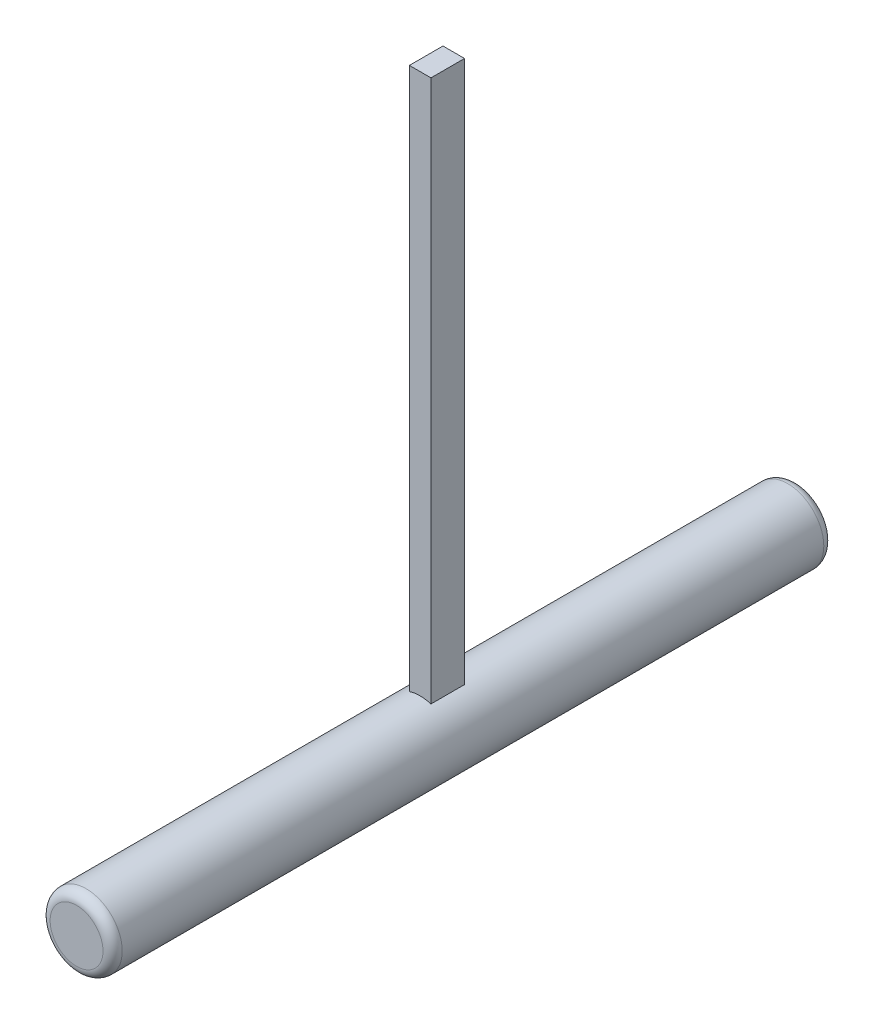
SolidWorks part; units mm, degrees
ref_plane "Front Plane" through (0, 0, 0) normal (0, 0, 1) x (1, 0, 0)
ref_plane "Top Plane" through (0, 0, 0) normal (0, 1, 0) x (1, 0, 0)
ref_plane "Right Plane" through (0, 0, 0) normal (1, 0, 0) x (0, 0, -1)
sketch "Sketch1" plane through (0, 0, 0) normal (0, 0, 1) x (1, 0, 0)
  circle A0 centre (0, 0) radius 7.5
  dimension "D1" = 15
extrude "Boss-Extrude1" add sketch "Sketch1" along normal blind 150
fillet "Fillet1" radius 2 2 edges at (7.5, 0, 0) (7.5, 0, 150)
ref_plane "Plane1" through (0, 120, 0) normal (0, 1, 0) x (1, 0, 0)
sketch "Sketch3" plane through (0, 120, 0) normal (0, 1, 0) x (1, 0, 0)
  line L0 (0, 0) -> (0, -150) construction
  line L1 (-2.245, -71.505) -> (2.245, -71.505)
  line L2 (-2.245, -71.505) -> (-2.245, -78.495)
  line L3 (-2.245, -78.495) -> (2.245, -78.495)
  line L4 (2.245, -71.505) -> (2.245, -78.495)
  line L5 (-2.245, -71.505) -> (2.245, -78.495) construction
  line L6 (-2.245, -78.495) -> (2.245, -71.505) construction
  line L7 (-5.5, -150) -> (5.5, -150) construction
  point P0 (0, -75)
  point P14 (0, -75)
  dimension "D1" = 4.49
  dimension "D2" = 6.99
extrude "Boss-Extrude2" add sketch "Sketch3" against normal up to surface (112.8439 mm away)
